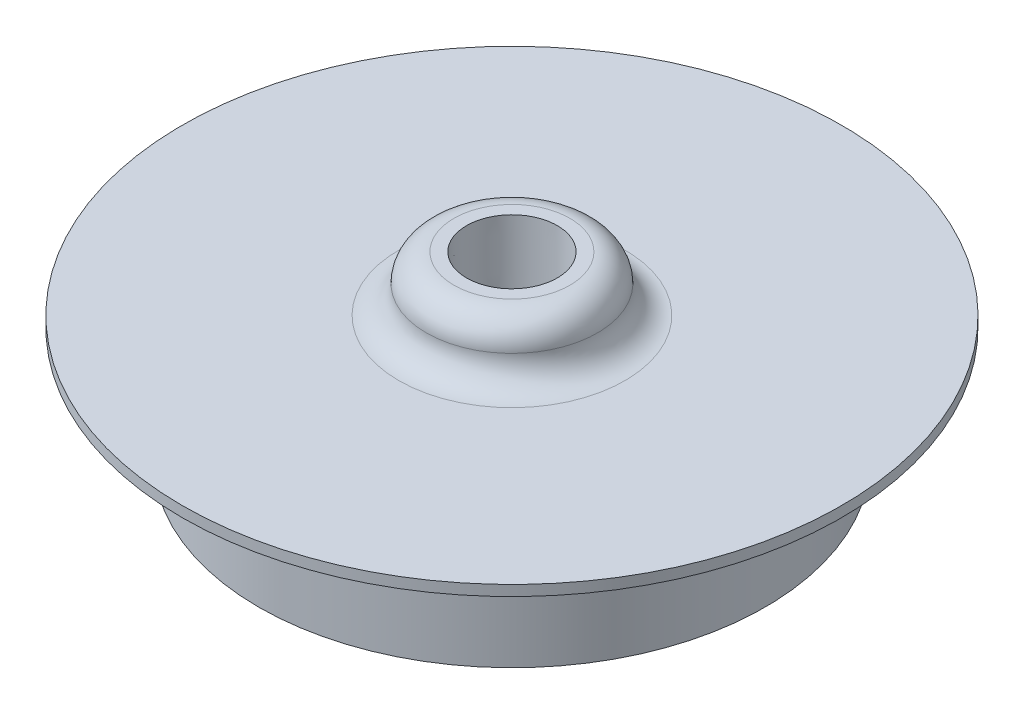
SolidWorks part; units mm, degrees
material "6063-T6"
ref_plane "Front Plane" through (0, 0, 0) normal (0, 0, 1) x (1, 0, 0)
ref_plane "Top Plane" through (0, 0, 0) normal (0, 1, 0) x (1, 0, 0)
ref_plane "Right Plane" through (0, 0, 0) normal (1, 0, 0) x (0, 0, -1)
ref_axis "Axis1" through (0, 55, 0) along (0, -1, 0)
sketch "Sketch1" plane through (0, 0, 0) normal (0, 0, 1) x (1, 0, 0)
  line L0 (-49.784, 0) -> (-39.8399, 0)
  line L1 (0, 55) -> (0, -55) construction
  line L2 (-49.784, 0) -> (-49.784, 1.5875)
  line L3 (-5.588, 9.906) -> (-8.763, 9.906)
  line L5 (-5.588, 9.906) -> (-5.588, 0)
  line L6 (-5.588, 0) -> (0, 0) construction
  line L7 (-49.784, 0) -> (-49.784, 1.5875) construction
  line L8 (-5.588, 1.5875) -> (-5.588, 0) construction
  line L9 (-38.2524, -1.5875) -> (-38.2524, -17.4625)
  line L10 (-38.2524, -17.4625) -> (-35.0774, -17.4625)
  line L11 (-35.0774, -17.4625) -> (-35.0774, -3.175)
  line L12 (-31.9024, 0) -> (-5.588, 0)
  line L13 (0, -201000) -> (0, 249000) construction
  line L14 (-49.784, 1.5875) -> (-17.0815, 1.5875)
  arc A0 (-35.0774, -3.175) -> (-31.9024, 0) centre (-31.9024, -3.175) cw
  arc A1 (-38.2524, -1.5875) -> (-39.8399, 0) centre (-39.8399, -1.5875) ccw
  arc A2 (-17.0815, 1.5875) -> (-12.9223, 5.7467) centre (-17.0815, 5.7467) ccw
  arc A3 (-8.763, 9.906) -> (-12.9223, 5.7467) centre (-8.763, 5.7467) ccw
  point P18 (-35.0774, 0)
  dimension "D4" = 3.175
  dimension "D5" = 1.5875
  dimension "D1" = 3.175
  dimension "D2" = 38.2524
  dimension "D3" = 17.4625
  dimension "D6" = 1.5875
  dimension "D7" = 3.175
  dimension "D8" = 9.906
revolve "Revolve1" add sketch "Sketch1" angle 360 about axis through (0, 55, 0) along (0, -1, 0)
hole_wizard "1/4 NPT Tapped Hole1" positions "Sketch4" profile "Sketch5" size "1/4" standard "ANSI Inch" end condition through all
sketch "Sketch4" plane through (0, 9.906, 0) normal (0, 1, 0) x (1, 0, 0)
  point P0 (0, 0)
sketch "Sketch5" plane through (0, 9.906, 0) normal (1, 0, 0) x (0, 0, 1)
  line L0 (0, 0) -> (0, 27.3685)
  line L1 (0, 27.3685) -> (5.5626, 27.3685)
  line L2 (-6.558, 9.906) -> (-6.8546, 0) construction
  line L3 (5.5626, 27.3685) -> (5.5626, 9.906)
  line L4 (5.5626, 9.906) -> (6.558, 9.906)
  line L5 (6.558, 9.906) -> (6.8546, 0)
  line L7 (6.8546, 0) -> (0, 0)
  line L8 (0, -6.35) -> (0, 107.95) construction
  line L11 (-5.5626, 9.906) -> (-6.558, 9.906) construction
  dimension "Thru Tap Drill Dia." = 11.1252
  dimension "Thru Tap Drill Depth" = 27.3685
  dimension "Thread Dia." = 13.7092
  dimension "Thread Angle" = 3.43
  dimension "Thread Depth" = 9.906
equation "\"D3@Sketch1\"=0.5+0.125+0.0625"
